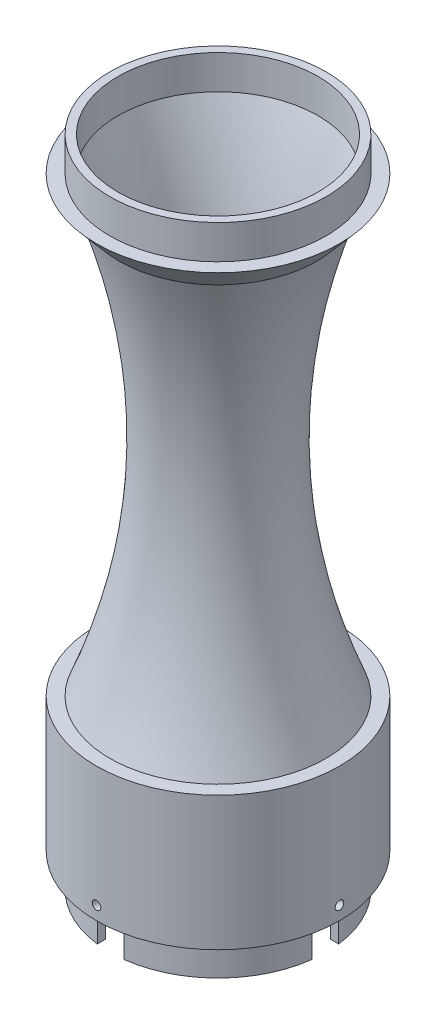
SolidWorks part; units mm, degrees
ref_plane "Front Plane" through (0, 0, 0) normal (0, 0, 1) x (1, 0, 0)
ref_plane "Top Plane" through (0, 0, 0) normal (0, 1, 0) x (1, 0, 0)
ref_plane "Right Plane" through (0, 0, 0) normal (1, 0, 0) x (0, 0, -1)
sketch "Sketch1" plane through (0, 0, 0) normal (0, 0, 1) x (1, 0, 0)
  line L4 (0, 189) -> (0, 201.7)
  line L5 (0, 201.7) -> (-3, 201.7)
  line L7 (-3, 201.7) -> (-3, 189)
  line L9 (-8, 189) -> (-3, 189)
  line L11 (-8, -30) -> (-3, -30)
  line L12 (-3, -30) -> (-3, -42.7)
  line L13 (0, -30) -> (0, 20)
  line L15 (0, -42.7) -> (0, -30)
  line L16 (-8, 189) -> (0.5702, 179)
  line L17 (-3, -42.7) -> (0, -42.7)
  line L18 (-3, 20) -> (-8, 20)
  line L19 (37.4027, -40) -> (37.4027, 199)
  line L20 (-8, 20) -> (-8, -30)
  spline S0 degree 3 poles (-3, 20) (17.5185, 71.9279) (18.7085, 124.9279) (0.5702, 179) knots 0 0 0 0 0.942 0.942 0.942 0.942
  spline S1 degree 2 poles (0, 20) (32.6727, 102.6878) (0, 189) knots 0 0 0 1 1 1
  dimension "D5" = 5
  dimension "D15" = 173.1223
  dimension "D16" = 40
  dimension "D1" = 50
  dimension "D2" = 3
  dimension "D3" = 12.7
  dimension "D4" = 219
  dimension "D6" = 3
  dimension "D7" = 5
  dimension "D8" = 37.4027
  dimension "D9" = 12.7
  dimension "D10" = 15
  dimension "D11" = 109.5
  dimension "D12" = 10
  dimension "D13" = 3
  dimension "D14" = 3.5702
  dimension "D17" = 239
revolve "Revolve1" add sketch "Sketch1" angle 360 about L19
sketch "Sketch2" plane through (0, -42.7, 0) normal (0, -1, 0) x (1, 0, 0)
  line L0 (25.4059, 5) -> (-3, 5)
  line L1 (25.4059, -5) -> (-3, -5)
  line L2 (-3, 5) -> (-3, -5)
  line L3 (42.4027, 11.9968) -> (42.4027, 40.4027)
  line L4 (32.4027, 11.9968) -> (32.4027, 40.4027)
  line L5 (42.4027, 40.4027) -> (32.4027, 40.4027)
  line L6 (49.3995, -5) -> (77.8053, -5)
  line L7 (49.3995, 5) -> (77.8053, 5)
  line L8 (77.8053, -5) -> (77.8053, 5)
  line L9 (32.4027, -11.9968) -> (32.4027, -40.4027)
  line L10 (42.4027, -11.9968) -> (42.4027, -40.4027)
  line L11 (32.4027, -40.4027) -> (42.4027, -40.4027)
  arc A1 (25.4059, -5) -> (32.4027, -11.9968) centre (37.4027, 0) ccw
  circle A2 centre (37.4027, 0) radius 40.4027 construction
  arc A3 (32.4027, 11.9968) -> (25.4059, 5) centre (37.4027, 0) ccw
  arc A4 (49.3995, 5) -> (42.4027, 11.9968) centre (37.4027, 0) ccw
  arc A5 (42.4027, -11.9968) -> (49.3995, -5) centre (37.4027, 0) ccw
  point P24 (37.4027, 0)
  dimension "D1" = 10
  dimension "D4" = 12.9971
  dimension "D2" = 5
  dimension "D3" = 4
extrude "Cut-Extrude1" cut sketch "Sketch2" against normal blind 22.7
sketch "Sketch3" plane through (-3, 0, 0) normal (1, 0, 0) x (0, 0, -1)
  line L0 (5, -20) -> (5, -30) construction
  line L1 (-5, -20) -> (5, -20) construction
  circle A0 centre (0, -25) radius 1.6
  dimension "D1" = 5
  dimension "D2" = 5
extrude "Cut-Extrude2" cut sketch "Sketch3" against normal through all
ref_axis "Axis1" through (37.4027, 20, 0) along (0, -1, 0)
pattern_circular "CirPattern1" count 4 over 360 about axis through (37.4027, 20, 0) along (0, -1, 0) of "Cut-Extrude2"
